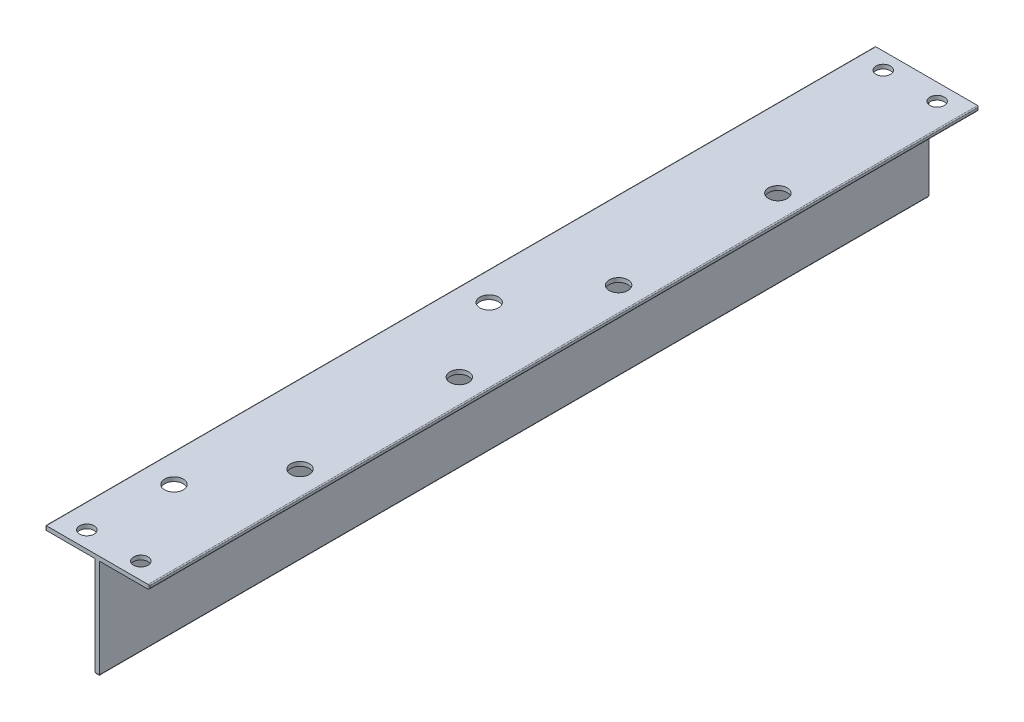
SolidWorks part; units mm, degrees
ref_plane "Front Plane" through (0, 0, 0) normal (0, 0, 1) x (1, 0, 0)
ref_plane "Top Plane" through (0, 0, 0) normal (0, 1, 0) x (1, 0, 0)
ref_plane "Right Plane" through (0, 0, 0) normal (1, 0, 0) x (0, 0, -1)
sketch "Sketch1" plane through (0, 0, 0) normal (0, 0, 1) x (1, 0, 0)
  line L0 (0, 0) -> (0, 24)
  line L1 (0, 24) -> (-12, 24)
  line L2 (-12, 24) -> (-12, 25)
  line L3 (-12, 25) -> (13, 25)
  line L4 (13, 25) -> (13, 24)
  line L5 (13, 24) -> (1, 24)
  line L6 (1, 24) -> (1, 0)
  line L7 (1, 0) -> (0, 0)
extrude "Extrude1" add sketch "Sketch1" along normal blind 200
sketch "Sketch3" plane through (0, 24, 0) normal (0, -1, 0) x (1, 0, 0)
  line L0 (7, 200) -> (7, 0) construction
  line L2 (1, 0) -> (13, 0) construction
  line L3 (-6, 200) -> (-6, 0) construction
  line L4 (-12, 200) -> (0, 200) construction
  line L5 (-12, 0) -> (0, 0) construction
  point P2 (7, 4)
  point P3 (-6, 196)
  point P7 (7, 196)
  point P13 (-6, 4)
  point P14 (7, 157.6)
fillet "Fillet1" radius 0.25 12 edges at (0, 0, 100) (0.5, 0, 200) (1, 0, 100) (0.5, 0, 0) (13, 24, 100) (13, 24.5, 200) (13, 25, 100) (13, 24.5, 0) (-12, 25, 100) (-12, 24.5, 200) (-12, 24, 100) (-12, 24.5, 0)
hole_wizard "Ø3.5 (3.5) Diameter Hole1" positions "3DSketch1" profile "Sketch5" hole size "Ø3.5" standard "DIN" end condition through all
sketch3d "3DSketch1"
  point P0 (-6, 24, 196)
  point P3 (7, 24, 196)
  point P7 (-6, 24, 4)
  point P10 (7, 24, 4)
sketch "Sketch5" plane through (-6, 24, 196) normal (1, 0, 0) x (0, 0, -1)
  line L0 (0, 0) -> (0, 1)
  line L1 (0, 1) -> (1.75, 1)
  line L2 (1.75, 1) -> (1.75, 0)
  line L5 (1.75, 0) -> (0, 0)
  line L11 (0, -6.35) -> (0, 107.95) construction
  dimension "Thru Hole Dia." = 3.5
  dimension "Thru Hole Depth" = 1
sketch "Sketch6" plane through (0, 25, 0) normal (0, 1, 0) x (1, 0, 0)
  line L0 (12.75, -176) -> (-11.75, -176) construction
  line L1 (12.75, -200) -> (12.75, 0) construction
  line L2 (-11.75, 0) -> (-11.75, -200) construction
  line L3 (12.75, -100) -> (-11.75, -100) construction
  point P8 (-5, -176)
  point P9 (-5, -100)
hole_wizard "Ø4.5 (4.5) Diameter Hole1" positions "3DSketch3" profile "Sketch9" hole size "Ø4.5" standard "DIN"
sketch3d "3DSketch3"
  point P0 (-5, 25, 176)
  point P3 (-5, 25, 100)
sketch "Sketch9" plane through (-5, 25, 176) normal (1, 0, 0) x (0, 0, 1)
  line L0 (0, 0) -> (0, 2.3519)
  line L1 (0, 2.3519) -> (2.25, 1)
  line L2 (2.25, 1) -> (2.25, 0)
  line L5 (2.25, 0) -> (0, 0)
  line L10 (0, 2.3519) -> (-2.25, 1) construction
  line L11 (0, -6.35) -> (0, 107.95) construction
  dimension "Hole Dia." = 4.5
  dimension "Hole Depth" = 1
  dimension "Drill Angle" = 118
hole_wizard "Ø4.5 (4.5) Diameter Hole2" positions "3DSketch4" profile "Sketch10" hole size "Ø4.5" standard "DIN"
sketch3d "3DSketch4"
  point P0 (7, 24, 157.6)
sketch "Sketch10" plane through (7, 24, 157.6) normal (1, 0, 0) x (0, 0, -1)
  line L0 (0, 0) -> (0, 2.3519)
  line L1 (0, 2.3519) -> (2.25, 1)
  line L2 (2.25, 1) -> (2.25, 0)
  line L5 (2.25, 0) -> (0, 0)
  line L10 (0, 2.3519) -> (-2.25, 1) construction
  line L11 (0, -6.35) -> (0, 107.95) construction
  dimension "Hole Dia." = 4.5
  dimension "Hole Depth" = 1
  dimension "Drill Angle" = 118
pattern_linear "LPattern1" count 4 spacing 38.4 along (0, 0, -1) of "Ø4.5 (4.5) Diameter Hole2"
